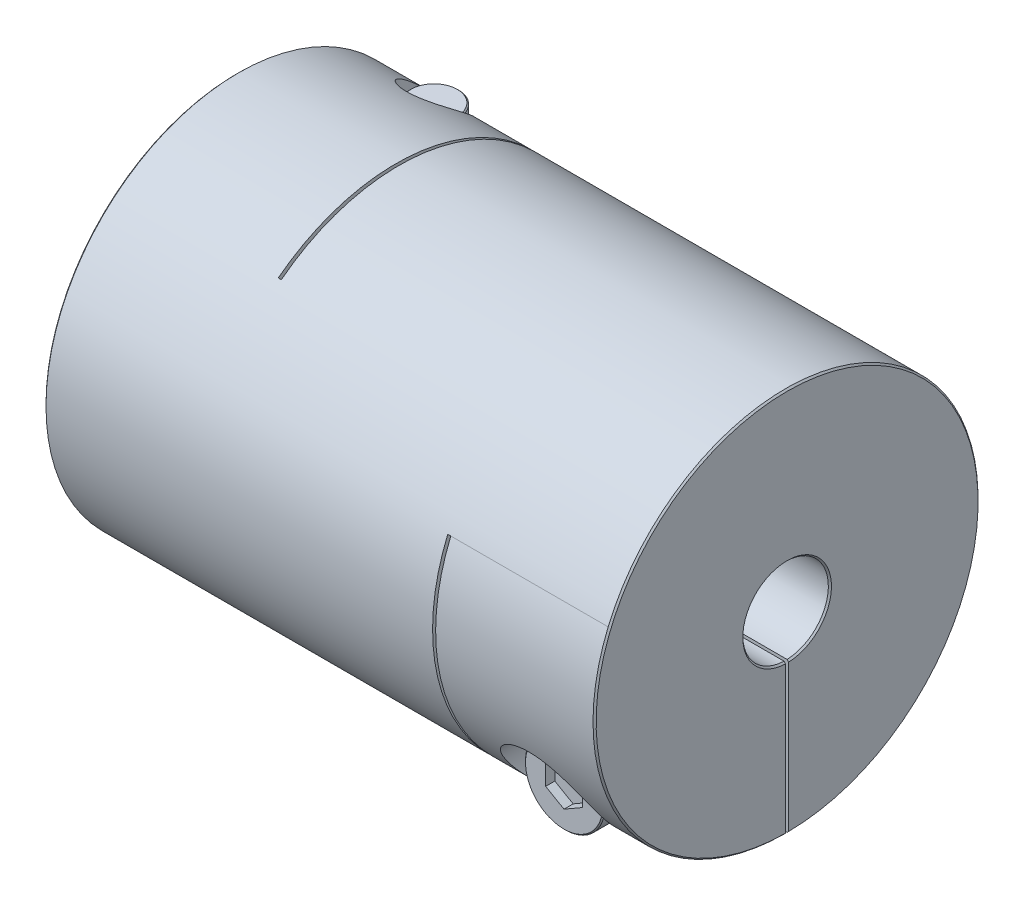
SolidWorks part; units mm, degrees
ref_plane "Front Plane" through (0, 0, 0) normal (0, 0, 1) x (1, 0, 0)
ref_plane "Top Plane" through (0, 0, 0) normal (0, 1, 0) x (1, 0, 0)
ref_plane "Right Plane" through (0, 0, 0) normal (1, 0, 0) x (0, 0, -1)
sketch "Sketch1" plane through (0, 0, 0) normal (1, 0, 0) x (0, 0, -1)
  circle A0 centre (0, 0) radius 31.5
  dimension "dim D" = 63
extrude "Boss-Extrude1" add sketch "Sketch1" along normal mid plane 90
sketch "Sketch2" plane through (45, 0, 0) normal (1, 0, 0) x (0, 0, -1)
  circle A0 centre (0, 0) radius 7
  dimension "dim D1" = 14
extrude "Cut-Extrude1" cut sketch "Sketch2" against normal through all
chamfer "Chamfer1" distance 0.254 angle 45 4 edges at (-45, 0, -7) (-45, 0, -31.5) (45, 0, -31.5) (45, 0, -7)
ref_plane "Plane2" through (0, -31.5, 0) normal (0, -1, 0) x (1, 0, 0)
ref_plane "L1" through (-32, 0, 0) normal (-1, 0, 0) x (0, 0, 1)
sketch "Sketch4" plane through (0, -31.5, 0) normal (0, -1, 0) x (1, 0, 0)
  line L0 (-44.746, -31.5) -> (44.746, -31.5) construction
  line L1 (-19, -31.5) -> (-18.5, -31.5)
  line L2 (-19, -31.5) -> (-19, 19.25)
  line L3 (-19, 19.25) -> (-18.5, 19.25)
  line L4 (-18.5, -31.5) -> (-18.5, 19.25)
  line L5 (-19, 7) -> (-19, 31.5) construction
  line L6 (44.746, 7) -> (-44.746, 7) construction
  line L7 (44.746, 31.5) -> (-44.746, 31.5) construction
  line L10 (-19, 19.25) -> (-45, 19.25) construction
  line L11 (-45, 31.246) -> (-45, -31.246) construction
  line L12 (-32, 10.2256) -> (-32, -10.2256) construction
  point P16 (-32, 19.25)
  dimension "D1" = 0.5
extrude "Cut-Extrude2" cut sketch "Sketch4" against normal through all
ref_plane "Plane4" through (0, 0, -31.5) normal (0, 0, -1) x (-1, 0, 0)
sketch "Sketch7" plane through (0, 0, -31.5) normal (0, 0, -1) x (-1, 0, 0)
  line L1 (-18.5, -31.5) -> (-19, -31.5)
  line L2 (-19, -31.5) -> (-19, 12.25)
  line L3 (-19, 12.25) -> (-18.5, 12.25)
  line L4 (-18.5, -31.5) -> (-18.5, 12.25)
  line L5 (45, 8.6487) -> (32, 8.6487) construction
  line L7 (-10.505, -31.5) -> (10.505, -31.5) construction
  line L8 (-44.746, -7) -> (18.5, -7) construction
  line L9 (45, -31.246) -> (45, 31.246) construction
  line L10 (-44.746, -7) -> (18.5, -7) construction
  line L11 (18.5, 24.9337) -> (19, 24.9337) construction
  line L12 (-19, 12.25) -> (-19, -31.5) construction
  line L14 (-44.746, -7) -> (18.5, -7) construction
  line L16 (-44.746, -7) -> (18.5, -7) construction
  line L17 (19, -31.5) -> (44.746, -31.5) construction
  line L18 (32, -10.2256) -> (32, 10.2256) construction
  line L19 (-44.746, -31.5) -> (-44.746, 31.5) construction
  line L20 (-45, 12.25) -> (-32, 12.25) construction
  line L21 (-45, 31.246) -> (-45, -31.246) construction
  line L22 (-32, 12.25) -> (-19, 12.25) construction
  line L23 (-44.746, -31.5) -> (-44.746, 31.5) construction
  line L24 (-44.746, -7) -> (-44.746, 31.5) construction
  line L25 (-44.746, -7) -> (18.5, -7) construction
  point P23 (-19, 12.25)
  point P33 (-44.746, 12.25)
extrude "Cut-Extrude3" cut sketch "Sketch7" against normal through all
sketch "Sketch8" plane through (0, 0, 0) normal (0, 1, 0) x (1, 0, 0)
  line L0 (-19, -19.25) -> (-19, 31.5) construction
  line L1 (-45, 31.5) -> (-19, 31.5)
  line L2 (-45, 31.5) -> (-45, 0)
  line L3 (-45, 0) -> (-19, 0)
  line L4 (-19, 31.5) -> (-19, 0)
  line L5 (10.505, 31.5) -> (-10.505, 31.5) construction
  line L6 (-45, 31.246) -> (-45, -31.246) construction
extrude "Cut-Extrude5" cut sketch "Sketch8" against normal mid plane 0.5
sketch "Sketch13" plane through (0, 0, 0) normal (0, 0, 1) x (1, 0, 0)
  line L0 (45, -31.246) -> (45, 31.246) construction
  line L1 (19, -31.5) -> (45, -31.5)
  line L2 (19, -31.5) -> (19, 0)
  line L3 (19, 0) -> (45, 0)
  line L4 (45, -31.5) -> (45, 0)
extrude "Cut-Extrude6" cut sketch "Sketch13" against normal mid plane 0.5
hole_wizard "CBORE for M8 SHCS1" positions "Sketch12" profile "Sketch11" counterbore size "M8" standard "Ansi Metric" end condition through all
sketch "Sketch12" plane through (0, -31.5, 0) normal (0, -1, 0) x (1, 0, 0)
  line L0 (-32, 10.2256) -> (-32, -10.2256) construction
  line L1 (-19, -6.9955) -> (-19, -31.499) construction
  line L2 (-19, -6.9955) -> (-19, -31.499)
  line L3 (-19, -19.2473) -> (-32, -19.2473) construction
  point P0 (-32, -19.2473)
sketch "Sketch11" plane through (-32, -31.5, -19.2473) normal (1, 0, 0) x (0, 0, -1)
  line L0 (0, 0) -> (0, 63)
  line L1 (0, 63) -> (4.5, 63)
  line L3 (4.5, 63) -> (4.5, 16)
  line L4 (4.5, 16) -> (7.5, 16)
  line L5 (7.5, 16) -> (7.5, 0)
  line L7 (7.5, 0) -> (0, 0)
  line L11 (0, -6.35) -> (0, 107.95) construction
  dimension "Thru Hole Dia." = 9
  dimension "Thru Hole Depth" = 63
  dimension "C'Bore Dia." = 15
  dimension "C'Bore Depth" = 16
ref_plane "Plane5" through (0, 0, 31.5) normal (0, 0, 1) x (1, 0, 0)
hole_wizard "CBORE for M8 SHCS2" positions "Sketch15" profile "Sketch14" counterbore size "M8" standard "Ansi Metric" end condition through all
sketch "Sketch15" plane through (0, 0, 31.5) normal (0, 0, 1) x (1, 0, 0)
  line L0 (-39.5, -15.5) -> (-24.5, -15.5) construction
  line L1 (-39.5, -15.5) -> (-24.5, -15.5)
  line L5 (0, 0) -> (0, 31.5) construction
  line L6 (-19, 31.5) -> (-44.746, 31.5) construction
  line L8 (39.5, -15.5) -> (24.5, -15.5)
  line L9 (32, -15.5) -> (32, -19.2473) construction
  line L11 (32, -31.499) -> (32, -6.9955) construction
  line L12 (44.746, -31.499) -> (19, -31.499) construction
  line L13 (19, -6.9955) -> (44.746, -6.9955) construction
  point P0 (32, -19.2473)
sketch "Sketch14" plane through (32, -19.2473, 31.5) normal (1, 0, 0) x (0, -1, 0)
  line L0 (0, 0) -> (0, 63)
  line L1 (0, 63) -> (4.5, 63)
  line L3 (4.5, 63) -> (4.5, 16)
  line L4 (4.5, 16) -> (7.5, 16)
  line L5 (7.5, 16) -> (7.5, 0)
  line L7 (7.5, 0) -> (0, 0)
  line L11 (0, -6.35) -> (0, 107.95) construction
  dimension "Thru Hole Dia." = 9
  dimension "Thru Hole Depth" = 63
  dimension "C'Bore Dia." = 15
  dimension "C'Bore Depth" = 16
sketch "Sketch16" plane through (0, 0, 15.5) normal (0, 0, 1) x (1, 0, 0)
  circle A0 centre (32, -19.2473) radius 6.5
  dimension "screw dia" = 13
extrude "Boss-Extrude2" add sketch "Sketch16" along normal blind 8 separate body
sketch "Sketch17" plane through (0, 0, 15.5) normal (0, 0, -1) x (-1, 0, 0)
  circle A0 centre (-32, -19.2473) radius 4
  dimension "D1" = 8
extrude "Boss-Extrude3" add sketch "Sketch17" along normal blind 39.5
chamfer "Chamfer2" distance 0.2 angle 45 3 edges at (28, -19.2473, -24) (38.5, -19.2473, 15.5) (38.5, -19.2473, 23.5)
sketch "Sketch18" plane through (0, 0, 23.5) normal (0, 0, 1) x (1, 0, 0)
  line L1 (32, -22.7114) -> (35, -20.9793)
  line L2 (35, -20.9793) -> (35, -17.5152)
  line L3 (35, -17.5152) -> (32, -15.7832)
  line L4 (32, -15.7832) -> (29, -17.5152)
  line L5 (29, -17.5152) -> (29, -20.9793)
  line L6 (29, -20.9793) -> (32, -22.7114)
  circle A0 centre (32, -19.2473) radius 3 construction
  dimension "hex" = 6
extrude "Cut-Extrude7" cut sketch "Sketch18" against normal blind 1.5
mirror "Mirror1" about plane through (0, 0, 0) normal (1, 0, 0) of bodies 121
pattern_circular "CirPattern1" count 2 every 90 about axis through (0, 0, 0) along (1, 0, 0) of bodies 122
delete or keep bodies "Body-Delete1" type delete bodies bodies 122
